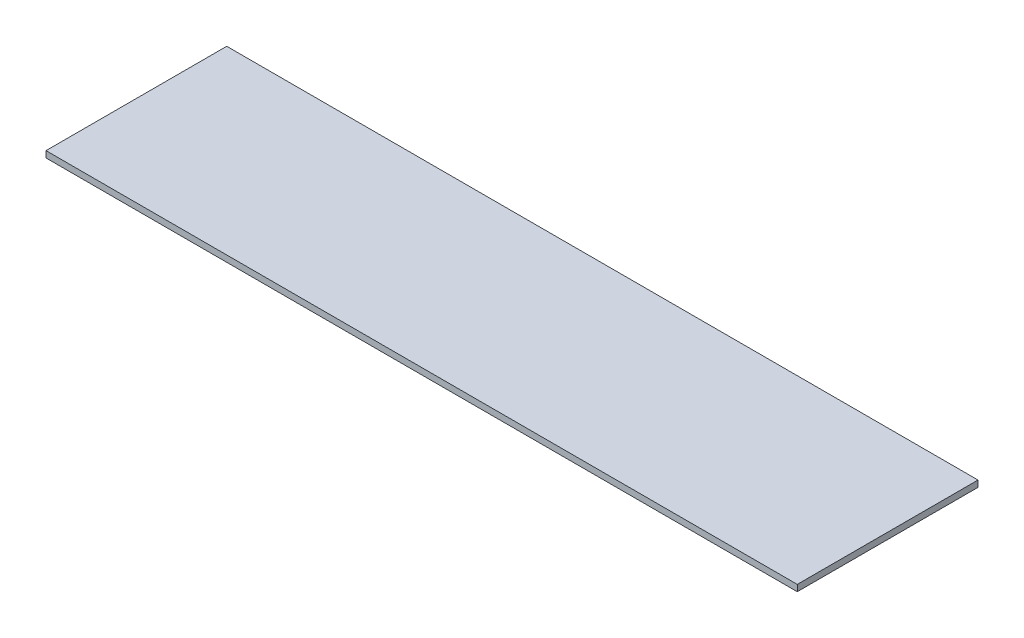
SolidWorks part; units mm, degrees
material "ABS"
ref_plane "Front Plane" through (0, 0, 0) normal (0, 0, 1) x (1, 0, 0)
ref_plane "Top Plane" through (0, 0, 0) normal (0, 1, 0) x (1, 0, 0)
ref_plane "Right Plane" through (0, 0, 0) normal (1, 0, 0) x (0, 0, -1)
sketch "Sketch1" plane through (0, 0, 0) normal (0, 1, 0) x (1, 0, 0)
  line L1 (0, 0) -> (2120, 0)
  line L2 (0, 0) -> (0, 510)
  line L3 (0, 510) -> (2120, 510)
  line L4 (2120, 0) -> (2120, 510)
  dimension "D1" = 510
  dimension "D2" = 2120
extrude "Boss-Extrude1" add sketch "Sketch1" along normal blind 18
